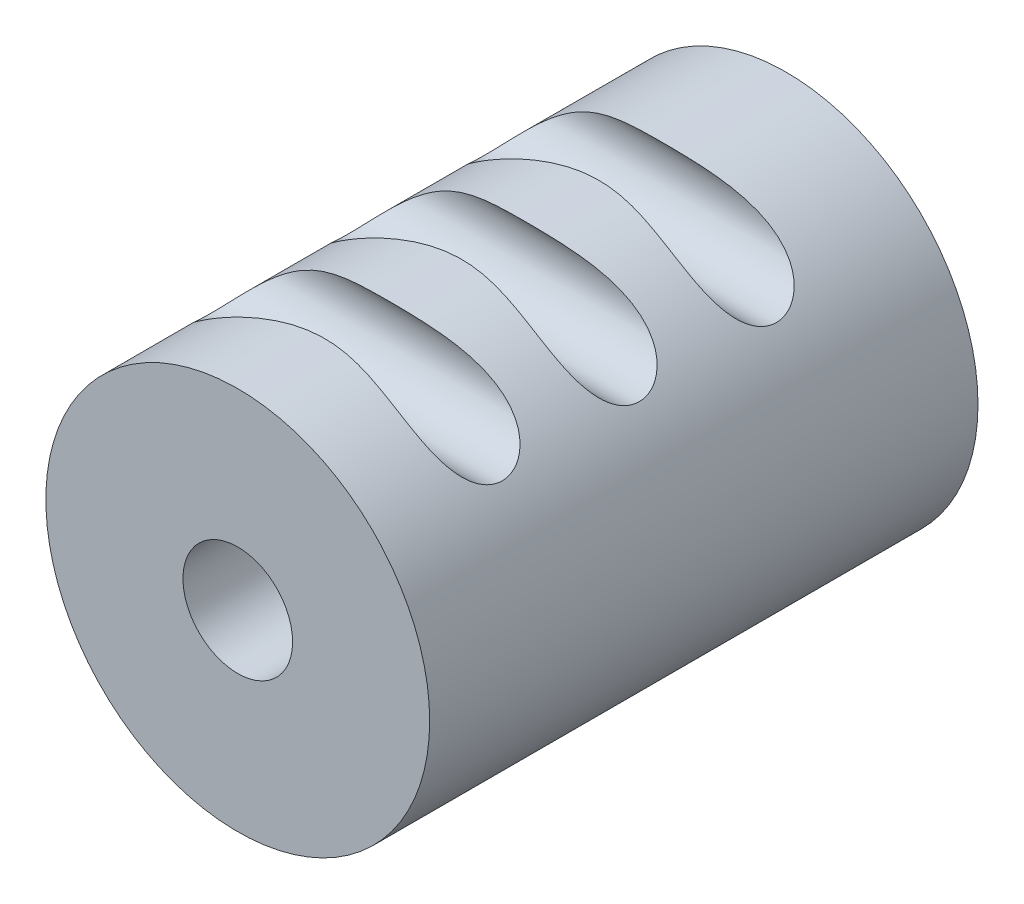
SolidWorks part; units mm, degrees
ref_plane "Front Plane" through (0, 0, 0) normal (0, 0, 1) x (1, 0, 0)
ref_plane "Top Plane" through (0, 0, 0) normal (0, 1, 0) x (1, 0, 0)
ref_plane "Right Plane" through (0, 0, 0) normal (1, 0, 0) x (0, 0, -1)
sketch "Sketch1" plane through (0, 0, 0) normal (0, 0, 1) x (1, 0, 0)
  circle A0 centre (0, 0) radius 4
  dimension "D1" = 8
extrude "Extrude-Thin1" add sketch "Sketch1" along normal blind 40 thin
sketch "Sketch2" plane through (0, 0, 0) normal (1, 0, 0) x (0, 0, -1)
  circle A0 centre (-31.3123, 12.1367) radius 3
  circle A1 centre (-21.3123, 12.1367) radius 3
  circle A2 centre (-11.3123, 12.1367) radius 3
  circle A3 centre (-21.3123, -12.8633) radius 3
  circle A4 centre (-11.3123, -12.8633) radius 3
  circle A5 centre (-31.3123, -12.8633) radius 3
  dimension "D1" = 3
  dimension "D2" = 2
extrude "Cut-Extrude1" cut sketch "Sketch2" against normal through all both and the other way through all
